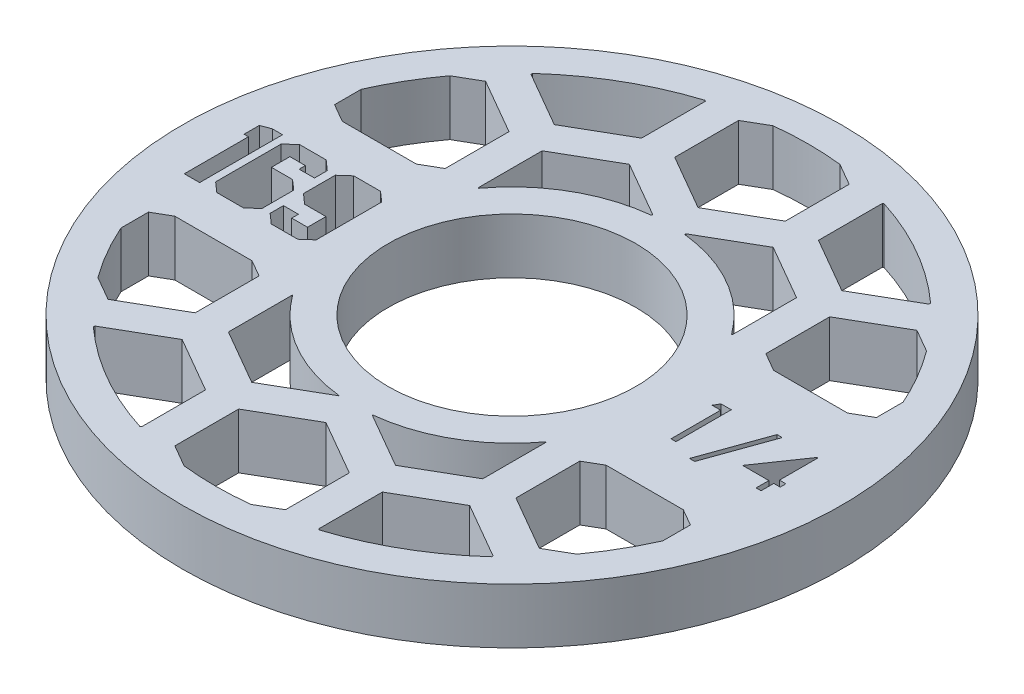
SolidWorks part; units mm, degrees
ref_plane "Front Plane" through (0, 0, 0) normal (0, 0, 1) x (1, 0, 0)
ref_plane "Top Plane" through (0, 0, 0) normal (0, 1, 0) x (1, 0, 0)
ref_plane "Right Plane" through (0, 0, 0) normal (1, 0, 0) x (0, 0, -1)
sketch "Sketch1" plane through (0, 0, 0) normal (0, 1, 0) x (1, 0, 0)
  circle A0 centre (0, 0) radius 14.224
  circle A1 centre (0, 0) radius 37.846
  dimension "D1" = 28.448
  dimension "D2" = 75.692
extrude "Boss-Extrude1" add sketch "Sketch1" along normal blind 6.35
sketch "Sketch2" plane through (0, 6.35, 0) normal (0, 1, 0) x (1, 0, 0)
  line L0 (-14.224, 0) -> (-37.846, 0) construction
  line L1 (-14.224, -4.7625) -> (-37.846, -4.7625) construction
  line L2 (14.224, 0) -> (37.846, 0) construction
  line L3 (14.224, -3.175) -> (37.846, -3.175) construction
  circle A0 centre (0, 0) radius 14.224 construction
  circle A1 centre (0, 0) radius 37.846 construction
  text T0 "169" font "Jersey M54" height 9.525
  text T1 "1/4" font "Century Gothic" height 6.35
  dimension "D1" = 4.7625
  dimension "D2" = 3.175
extrude "Cut-Extrude1" cut sketch "Sketch2" against normal through all both and the other way through all
sketch "Sketch3" plane through (0, 6.35, 0) normal (0, 1, 0) x (1, 0, 0)
  line L0 (0, -9.525) -> (0, 9.525)
  line L1 (36.6278, 9.525) -> (-36.6278, 9.525)
  line L2 (36.6278, -9.525) -> (-36.6278, -9.525)
  line L3 (16.51, -7.3323) -> (22.86, -3.6662)
  line L4 (0, -7.3323) -> (6.35, -3.6662)
  line L5 (6.35, -3.6662) -> (6.35, 3.6662)
  line L6 (6.35, 3.6662) -> (0, 7.3323)
  line L7 (0, 7.3323) -> (-6.35, 3.6662)
  line L8 (-6.35, 3.6662) -> (-6.35, -3.6662)
  line L9 (-6.35, -3.6662) -> (0, -7.3323)
  line L10 (8.255, -21.6304) -> (14.605, -17.9643)
  line L11 (14.605, -17.9643) -> (14.605, -10.6319)
  line L12 (14.605, -10.6319) -> (8.255, -6.9657)
  line L13 (8.255, -6.9657) -> (1.905, -10.6319)
  line L14 (1.905, -10.6319) -> (1.905, -17.9643)
  line L15 (1.905, -17.9643) -> (8.255, -21.6304)
  line L16 (22.86, -3.6662) -> (22.86, 3.6662)
  line L17 (22.86, 3.6662) -> (16.51, 7.3323)
  line L18 (16.51, 7.3323) -> (10.16, 3.6662)
  line L19 (10.16, 3.6662) -> (10.16, -3.6662)
  line L20 (10.16, -3.6662) -> (16.51, -7.3323)
  line L21 (24.765, -21.6304) -> (31.115, -17.9643)
  line L22 (31.115, -17.9643) -> (31.115, -10.6319)
  line L23 (31.115, -10.6319) -> (24.765, -6.9657)
  line L24 (24.765, -6.9657) -> (18.415, -10.6319)
  line L25 (18.415, -10.6319) -> (18.415, -17.9643)
  line L26 (18.415, -17.9643) -> (24.765, -21.6304)
  line L27 (33.02, -7.3323) -> (39.37, -3.6662)
  line L28 (39.37, -3.6662) -> (39.37, 3.6662)
  line L29 (39.37, 3.6662) -> (33.02, 7.3323)
  line L30 (33.02, 7.3323) -> (26.67, 3.6662)
  line L31 (26.67, 3.6662) -> (26.67, -3.6662)
  line L32 (26.67, -3.6662) -> (33.02, -7.3323)
  line L33 (41.275, -21.6304) -> (47.625, -17.9643)
  line L34 (47.625, -17.9643) -> (47.625, -10.6319)
  line L35 (47.625, -10.6319) -> (41.275, -6.9657)
  line L36 (41.275, -6.9657) -> (34.925, -10.6319)
  line L37 (34.925, -10.6319) -> (34.925, -17.9643)
  line L38 (34.925, -17.9643) -> (41.275, -21.6304)
  line L39 (-16.51, -7.3323) -> (-10.16, -3.6662)
  line L40 (-10.16, -3.6662) -> (-10.16, 3.6662)
  line L41 (-10.16, 3.6662) -> (-16.51, 7.3323)
  line L42 (-16.51, 7.3323) -> (-22.86, 3.6662)
  line L43 (-22.86, 3.6662) -> (-22.86, -3.6662)
  line L44 (-22.86, -3.6662) -> (-16.51, -7.3323)
  line L45 (-8.255, -21.6304) -> (-1.905, -17.9643)
  line L46 (-1.905, -17.9643) -> (-1.905, -10.6319)
  line L47 (-1.905, -10.6319) -> (-8.255, -6.9657)
  line L48 (-8.255, -6.9657) -> (-14.605, -10.6319)
  line L49 (-14.605, -10.6319) -> (-14.605, -17.9643)
  line L50 (-14.605, -17.9643) -> (-8.255, -21.6304)
  line L51 (-33.02, -7.3323) -> (-26.67, -3.6662)
  line L52 (-26.67, -3.6662) -> (-26.67, 3.6662)
  line L53 (-26.67, 3.6662) -> (-33.02, 7.3323)
  line L54 (-33.02, 7.3323) -> (-39.37, 3.6662)
  line L55 (-39.37, 3.6662) -> (-39.37, -3.6662)
  line L56 (-39.37, -3.6662) -> (-33.02, -7.3323)
  line L57 (-24.765, -21.6304) -> (-18.415, -17.9643)
  line L58 (-18.415, -17.9643) -> (-18.415, -10.6319)
  line L59 (-18.415, -10.6319) -> (-24.765, -6.9657)
  line L60 (-24.765, -6.9657) -> (-31.115, -10.6319)
  line L61 (-31.115, -10.6319) -> (-31.115, -17.9643)
  line L62 (-31.115, -17.9643) -> (-24.765, -21.6304)
  line L63 (0, 21.3697) -> (6.35, 25.0358)
  line L64 (6.35, 25.0358) -> (6.35, 32.3682)
  line L65 (6.35, 32.3682) -> (0, 36.0343)
  line L66 (0, 36.0343) -> (-6.35, 32.3682)
  line L67 (-6.35, 32.3682) -> (-6.35, 25.0358)
  line L68 (-6.35, 25.0358) -> (0, 21.3697)
  line L69 (8.255, 7.0716) -> (14.605, 10.7377)
  line L70 (14.605, 10.7377) -> (14.605, 18.0701)
  line L71 (14.605, 18.0701) -> (8.255, 21.7363)
  line L72 (8.255, 21.7363) -> (1.905, 18.0701)
  line L73 (1.905, 18.0701) -> (1.905, 10.7377)
  line L74 (1.905, 10.7377) -> (8.255, 7.0716)
  line L75 (-33.02, 21.3697) -> (-26.67, 25.0358)
  line L76 (-26.67, 25.0358) -> (-26.67, 32.3682)
  line L77 (-26.67, 32.3682) -> (-33.02, 36.0343)
  line L78 (-33.02, 36.0343) -> (-39.37, 32.3682)
  line L79 (-39.37, 32.3682) -> (-39.37, 25.0358)
  line L80 (-39.37, 25.0358) -> (-33.02, 21.3697)
  line L81 (-24.765, 7.0716) -> (-18.415, 10.7377)
  line L82 (-18.415, 10.7377) -> (-18.415, 18.0701)
  line L83 (-18.415, 18.0701) -> (-24.765, 21.7363)
  line L84 (-24.765, 21.7363) -> (-31.115, 18.0701)
  line L85 (-31.115, 18.0701) -> (-31.115, 10.7377)
  line L86 (-31.115, 10.7377) -> (-24.765, 7.0716)
  line L87 (-16.51, 21.3697) -> (-10.16, 25.0358)
  line L88 (-10.16, 25.0358) -> (-10.16, 32.3682)
  line L89 (-10.16, 32.3682) -> (-16.51, 36.0343)
  line L90 (-16.51, 36.0343) -> (-22.86, 32.3682)
  line L91 (-22.86, 32.3682) -> (-22.86, 25.0358)
  line L92 (-22.86, 25.0358) -> (-16.51, 21.3697)
  line L93 (-8.255, 7.0716) -> (-1.905, 10.7377)
  line L94 (-1.905, 10.7377) -> (-1.905, 18.0701)
  line L95 (-1.905, 18.0701) -> (-8.255, 21.7363)
  line L96 (-8.255, 21.7363) -> (-14.605, 18.0701)
  line L97 (-14.605, 18.0701) -> (-14.605, 10.7377)
  line L98 (-14.605, 10.7377) -> (-8.255, 7.0716)
  line L99 (16.51, 21.3697) -> (22.86, 25.0358)
  line L100 (22.86, 25.0358) -> (22.86, 32.3682)
  line L101 (22.86, 32.3682) -> (16.51, 36.0343)
  line L102 (16.51, 36.0343) -> (10.16, 32.3682)
  line L103 (10.16, 32.3682) -> (10.16, 25.0358)
  line L104 (10.16, 25.0358) -> (16.51, 21.3697)
  line L105 (24.765, 7.0716) -> (31.115, 10.7377)
  line L106 (31.115, 10.7377) -> (31.115, 18.0701)
  line L107 (31.115, 18.0701) -> (24.765, 21.7363)
  line L108 (24.765, 21.7363) -> (18.415, 18.0701)
  line L109 (18.415, 18.0701) -> (18.415, 10.7377)
  line L110 (18.415, 10.7377) -> (24.765, 7.0716)
  line L111 (33.02, 21.3697) -> (39.37, 25.0358)
  line L112 (39.37, 25.0358) -> (39.37, 32.3682)
  line L113 (39.37, 32.3682) -> (33.02, 36.0343)
  line L114 (33.02, 36.0343) -> (26.67, 32.3682)
  line L115 (26.67, 32.3682) -> (26.67, 25.0358)
  line L116 (26.67, 25.0358) -> (33.02, 21.3697)
  line L117 (41.275, 7.0716) -> (47.625, 10.7377)
  line L118 (47.625, 10.7377) -> (47.625, 18.0701)
  line L119 (47.625, 18.0701) -> (41.275, 21.7363)
  line L120 (41.275, 21.7363) -> (34.925, 18.0701)
  line L121 (34.925, 18.0701) -> (34.925, 10.7377)
  line L122 (34.925, 10.7377) -> (41.275, 7.0716)
  line L123 (0, -36.0343) -> (6.35, -32.3682)
  line L124 (6.35, -32.3682) -> (6.35, -25.0358)
  line L125 (6.35, -25.0358) -> (0, -21.3697)
  line L126 (0, -21.3697) -> (-6.35, -25.0358)
  line L127 (-6.35, -25.0358) -> (-6.35, -32.3682)
  line L128 (-6.35, -32.3682) -> (0, -36.0343)
  line L129 (8.255, -50.3324) -> (14.605, -46.6663)
  line L130 (14.605, -46.6663) -> (14.605, -39.3339)
  line L131 (14.605, -39.3339) -> (8.255, -35.6677)
  line L132 (8.255, -35.6677) -> (1.905, -39.3339)
  line L133 (1.905, -39.3339) -> (1.905, -46.6663)
  line L134 (1.905, -46.6663) -> (8.255, -50.3324)
  line L135 (-33.02, -36.0343) -> (-26.67, -32.3682)
  line L136 (-26.67, -32.3682) -> (-26.67, -25.0358)
  line L137 (-26.67, -25.0358) -> (-33.02, -21.3697)
  line L138 (-33.02, -21.3697) -> (-39.37, -25.0358)
  line L139 (-39.37, -25.0358) -> (-39.37, -32.3682)
  line L140 (-39.37, -32.3682) -> (-33.02, -36.0343)
  line L141 (-24.765, -50.3324) -> (-18.415, -46.6663)
  line L142 (-18.415, -46.6663) -> (-18.415, -39.3339)
  line L143 (-18.415, -39.3339) -> (-24.765, -35.6677)
  line L144 (-24.765, -35.6677) -> (-31.115, -39.3339)
  line L145 (-31.115, -39.3339) -> (-31.115, -46.6663)
  line L146 (-31.115, -46.6663) -> (-24.765, -50.3324)
  line L147 (-16.51, -36.0343) -> (-10.16, -32.3682)
  line L148 (-10.16, -32.3682) -> (-10.16, -25.0358)
  line L149 (-10.16, -25.0358) -> (-16.51, -21.3697)
  line L150 (-16.51, -21.3697) -> (-22.86, -25.0358)
  line L151 (-22.86, -25.0358) -> (-22.86, -32.3682)
  line L152 (-22.86, -32.3682) -> (-16.51, -36.0343)
  line L153 (-8.255, -50.3324) -> (-1.905, -46.6663)
  line L154 (-1.905, -46.6663) -> (-1.905, -39.3339)
  line L155 (-1.905, -39.3339) -> (-8.255, -35.6677)
  line L156 (-8.255, -35.6677) -> (-14.605, -39.3339)
  line L157 (-14.605, -39.3339) -> (-14.605, -46.6663)
  line L158 (-14.605, -46.6663) -> (-8.255, -50.3324)
  line L159 (16.51, -36.0343) -> (22.86, -32.3682)
  line L160 (22.86, -32.3682) -> (22.86, -25.0358)
  line L161 (22.86, -25.0358) -> (16.51, -21.3697)
  line L162 (16.51, -21.3697) -> (10.16, -25.0358)
  line L163 (10.16, -25.0358) -> (10.16, -32.3682)
  line L164 (10.16, -32.3682) -> (16.51, -36.0343)
  line L165 (24.765, -50.3324) -> (31.115, -46.6663)
  line L166 (31.115, -46.6663) -> (31.115, -39.3339)
  line L167 (31.115, -39.3339) -> (24.765, -35.6677)
  line L168 (24.765, -35.6677) -> (18.415, -39.3339)
  line L169 (18.415, -39.3339) -> (18.415, -46.6663)
  line L170 (18.415, -46.6663) -> (24.765, -50.3324)
  line L171 (33.02, -36.0343) -> (39.37, -32.3682)
  line L172 (39.37, -32.3682) -> (39.37, -25.0358)
  line L173 (39.37, -25.0358) -> (33.02, -21.3697)
  line L174 (33.02, -21.3697) -> (26.67, -25.0358)
  line L175 (26.67, -25.0358) -> (26.67, -32.3682)
  line L176 (26.67, -32.3682) -> (33.02, -36.0343)
  line L177 (41.275, -50.3324) -> (47.625, -46.6663)
  line L178 (47.625, -46.6663) -> (47.625, -39.3339)
  line L179 (47.625, -39.3339) -> (41.275, -35.6677)
  line L180 (41.275, -35.6677) -> (34.925, -39.3339)
  line L181 (34.925, -39.3339) -> (34.925, -46.6663)
  line L182 (34.925, -46.6663) -> (41.275, -50.3324)
  circle A0 centre (0, 0) radius 37.846 construction
  circle A1 centre (0, 0) radius 34.036
  circle A2 centre (0, 0) radius 18.034
  circle A3 centre (0, 0) radius 6.35 construction
  circle A4 centre (8.255, -14.2981) radius 6.35 construction
  point P4 (0, 0)
  point P10 (0, 9.525)
  point P13 (0, -9.525)
  dimension "D2" = 68.072
  dimension "D3" = 36.068
  dimension "D1" = 19.05
  dimension "D4" = 12.7
  dimension "D5" = 12.7
  dimension "D6" = 3.81
  dimension "D7" = 1.905
  dimension "D8" = 3
  dimension "D9" = 3
  dimension "D10" = 2
  dimension "D11" = 2
extrude "Cut-Extrude2" cut sketch "Sketch3" against normal through all both and the other way through all contours L84 A1 L85 L86 L1 L81 L82 L83 | L89 A1 L91 L92 L87 L88 | A2 L94 L95 L96 L97 L98 | L65 A1 L66 L67 L68 L63 L64 | A2 L69 L70 L71 L72 L73 | L100 A1 L102 L103 L104 L99 | L106 A1 L107 L108 L109 L110 L1 L105 | L21 A1 L22 L23 L2 L24 L25 L26 | A2 L14 L15 L10 L11 L12 | L164 A1 L160 L161 L162 L163 | L128 A1 L123 L124 L125 L126 L127 | A2 L48 L49 L50 L45 L46 | L151 A1 L147 L148 L149 L150 | L61 A1 L62 L57 L58 L59 L2 L60
